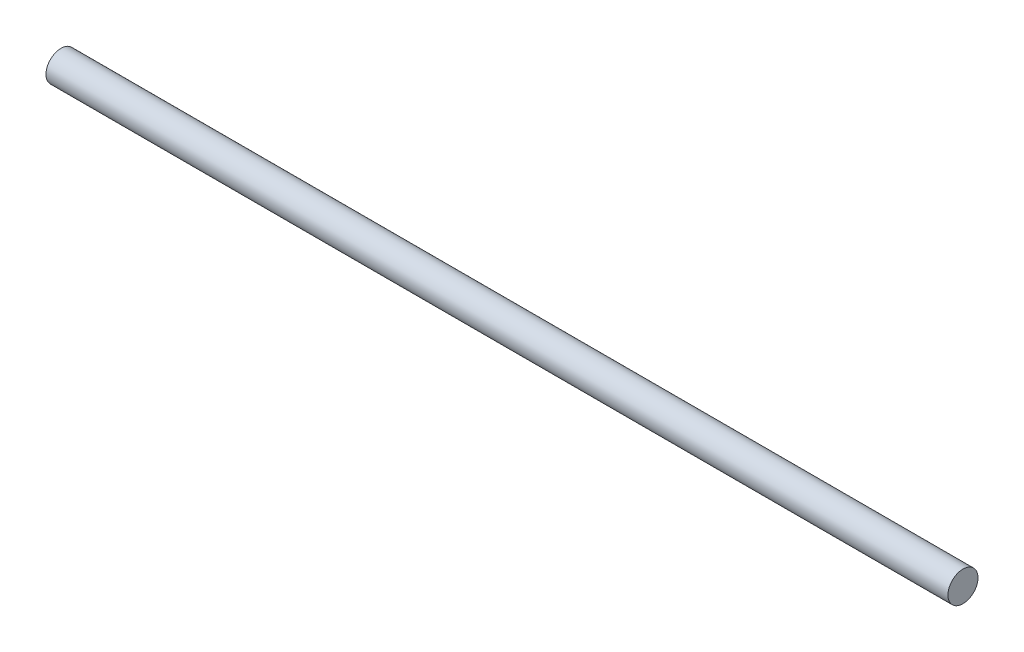
SolidWorks part; units mm, degrees
ref_plane "Front Plane" through (0, 0, 0) normal (0, 0, 1) x (1, 0, 0)
ref_plane "Top Plane" through (0, 0, 0) normal (0, 1, 0) x (1, 0, 0)
ref_plane "Right Plane" through (0, 0, 0) normal (1, 0, 0) x (0, 0, -1)
sketch "Sketch1" plane through (0, 0, 0) normal (1, 0, 0) x (0, 0, -1)
  circle A0 centre (0, 0) radius 2.5
  dimension "D1" = 5
extrude "Boss-Extrude1" add sketch "Sketch1" along normal blind 150
